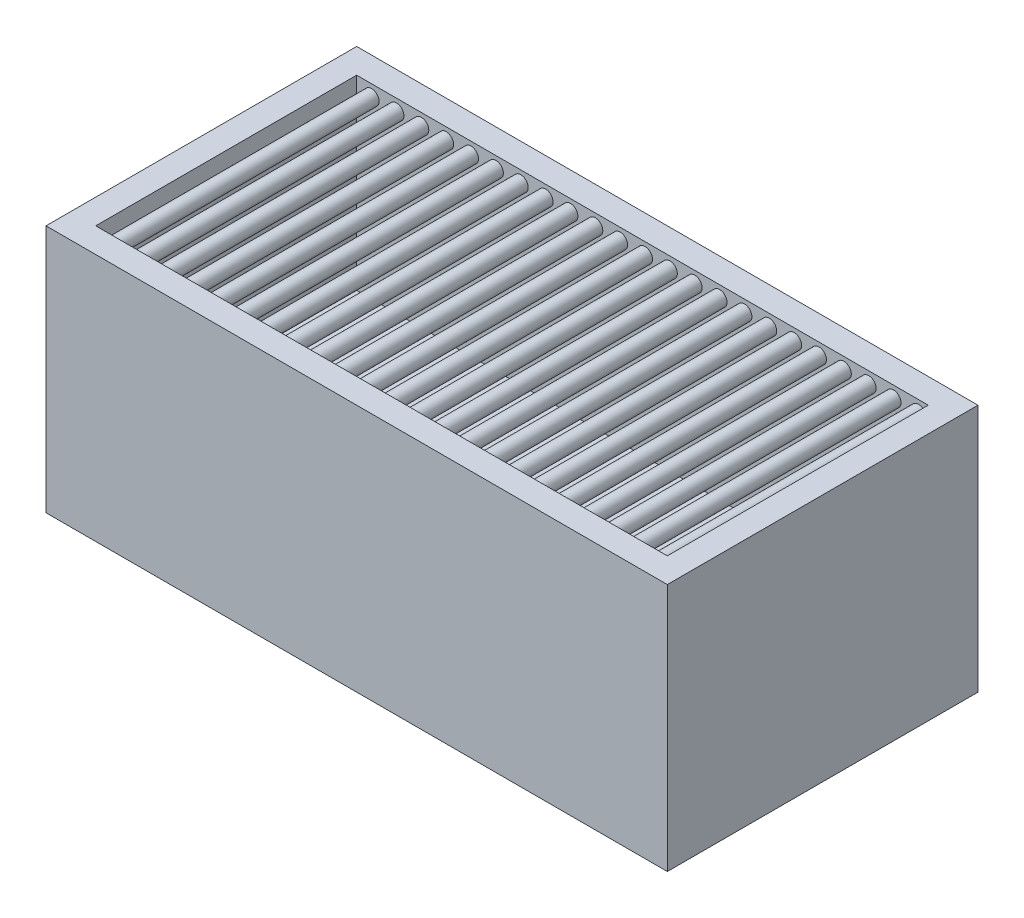
SolidWorks part; units mm, degrees
ref_plane "Front Plane" through (0, 0, 0) normal (0, 0, 1) x (1, 0, 0)
ref_plane "Top Plane" through (0, 0, 0) normal (0, 1, 0) x (1, 0, 0)
ref_plane "Right Plane" through (0, 0, 0) normal (1, 0, 0) x (0, 0, -1)
sketch "Sketch1" plane through (0, 0, 0) normal (0, 0, 1) x (1, 0, 0)
  line L1 (-25, 20) -> (25, 20)
  line L2 (-25, 20) -> (-25, 0)
  line L3 (-25, 0) -> (25, 0)
  line L4 (25, 20) -> (25, 0)
  point P4 (0, 0)
  dimension "D1" = 50
  dimension "D2" = 20
extrude "Boss-Extrude1" add sketch "Sketch1" along normal mid plane 25
sketch "Sketch2" plane through (0, 0, 0) normal (0, 1, 0) x (1, 0, 0)
  line L1 (23, -10.5) -> (-23, -10.5)
  line L2 (23, -10.5) -> (23, 10.5)
  line L3 (23, 10.5) -> (-23, 10.5)
  line L4 (-23, -10.5) -> (-23, 10.5)
  line L5 (23, -10.5) -> (-23, 10.5) construction
  line L6 (23, 10.5) -> (-23, -10.5) construction
  point P0 (0, 0)
  dimension "D1" = 46
  dimension "D2" = 21
extrude "Cut-Extrude1" cut sketch "Sketch2" against normal blind 15 from surface at 20 starting at face at (0, 20, 0)
sketch "Sketch3" plane through (0, 0, 0) normal (0, 0, 1) x (1, 0, 0)
  circle A0 centre (-21.795, 19.0651) radius 0.6
  circle A1 centre (-19.795, 19.0651) radius 0.6
  circle A2 centre (-17.795, 19.0651) radius 0.6
  circle A3 centre (-15.795, 19.0651) radius 0.6
  circle A4 centre (-13.795, 19.0651) radius 0.6
  circle A5 centre (-11.795, 19.0651) radius 0.6
  circle A6 centre (-9.795, 19.0651) radius 0.6
  circle A7 centre (-7.795, 19.0651) radius 0.6
  circle A8 centre (-5.795, 19.0651) radius 0.6
  circle A9 centre (-3.795, 19.0651) radius 0.6
  circle A10 centre (-1.795, 19.0651) radius 0.6
  circle A11 centre (0.205, 19.0651) radius 0.6
  circle A12 centre (2.205, 19.0651) radius 0.6
  circle A13 centre (4.205, 19.0651) radius 0.6
  circle A14 centre (6.205, 19.0651) radius 0.6
  circle A15 centre (8.205, 19.0651) radius 0.6
  circle A16 centre (10.205, 19.0651) radius 0.6
  circle A17 centre (12.205, 19.0651) radius 0.6
  circle A18 centre (14.205, 19.0651) radius 0.6
  circle A19 centre (16.205, 19.0651) radius 0.6
  circle A20 centre (18.205, 19.0651) radius 0.6
  circle A21 centre (20.205, 19.0651) radius 0.6
  circle A22 centre (22.205, 19.0651) radius 0.6
  dimension "D1" = 1.2
  dimension "D2" = 23
extrude "Boss-Extrude2" add sketch "Sketch3" along normal blind 21 from surface at -10.5 starting at face at (0, 12.5, -10.5)
